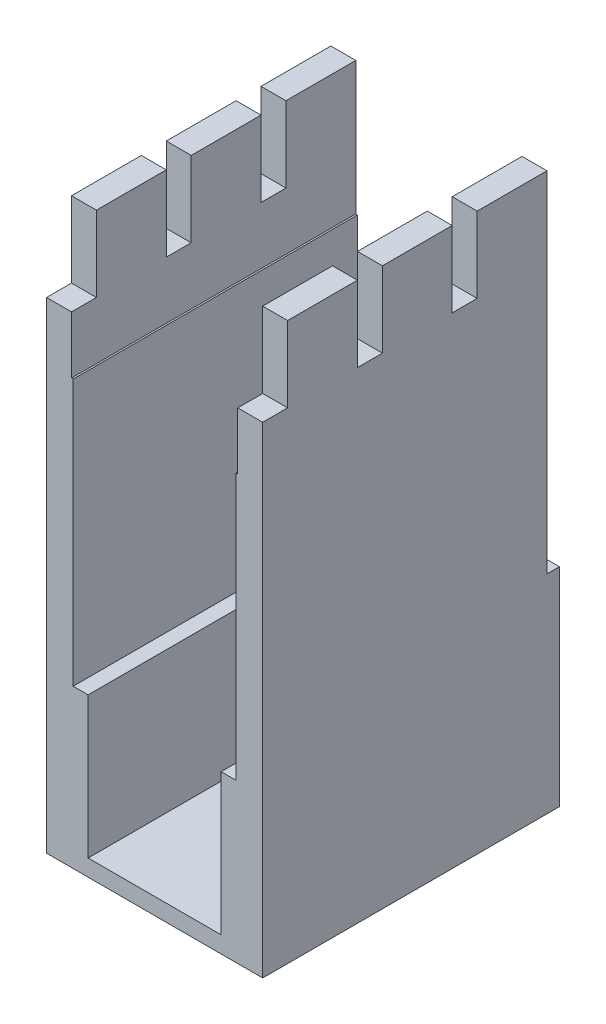
SolidWorks part; units mm, degrees
ref_plane "Front Plane" through (0, 0, 0) normal (0, 0, 1) x (1, 0, 0)
ref_plane "Top Plane" through (0, 0, 0) normal (0, 1, 0) x (1, 0, 0)
ref_plane "Right Plane" through (0, 0, 0) normal (1, 0, 0) x (0, 0, -1)
sketch "Sketch1" plane through (0, 0, 0) normal (0, 0, 1) x (1, 0, 0)
  line L0 (-13, 67) -> (-13, 0)
  line L1 (-13, 0) -> (13, 0)
  line L2 (13, 0) -> (13, 67)
  line L3 (13, 67) -> (10, 67)
  line L4 (10, 67) -> (10, 51)
  line L5 (10, 51) -> (9.8, 51)
  line L9 (-9.8, 51) -> (-10, 51)
  line L10 (-10, 51) -> (-10, 67)
  line L11 (-10, 67) -> (-13, 67)
  line L12 (-9.8, 51) -> (-9.8, 19)
  line L13 (-9.8, 19) -> (-8, 19)
  line L14 (-8, 19) -> (-8, 2)
  line L15 (9.8, 51) -> (9.8, 19)
  line L16 (9.8, 19) -> (8, 19)
  line L17 (8, 19) -> (8, 2)
  line L18 (-8, 2) -> (8, 2)
  point P11 (0, 0)
  point P25 (-11.5, 67)
  dimension "D1" = 2
  dimension "D2" = 3
  dimension "D3" = 20
  dimension "D4" = 19.6
  dimension "D5" = 16
  dimension "D6" = 17
  dimension "D7" = 32
  dimension "D8" = 65
extrude "Boss-Extrude1" add sketch "Sketch1" along normal blind 54
sketch "Sketch2" plane through (13, 0, 0) normal (1, 0, 0) x (0, 0, -1)
  line L0 (-54, 67) -> (0, 67) construction
  line L1 (-45.6, 67) -> (-42.6, 67)
  line L2 (-45.6, 67) -> (-45.6, 57.9)
  line L3 (-45.6, 57.9) -> (-42.6, 57.9)
  line L4 (-42.6, 67) -> (-42.6, 57.9)
  line L5 (-54, 62.45) -> (-45.6, 62.45) construction
  line L6 (-34.2, 67) -> (-31.2, 67)
  line L7 (-34.2, 67) -> (-34.2, 57.9)
  line L8 (-34.2, 57.9) -> (-31.2, 57.9)
  line L9 (-31.2, 67) -> (-31.2, 57.9)
  line L10 (-22.8, 67) -> (-19.8, 67)
  line L11 (-22.8, 67) -> (-22.8, 57.9)
  line L12 (-22.8, 57.9) -> (-19.8, 57.9)
  line L13 (-19.8, 67) -> (-19.8, 57.9)
  line L14 (-11.4, 67) -> (-8.4, 67)
  line L15 (-11.4, 67) -> (-11.4, 57.9)
  line L16 (-11.4, 57.9) -> (-8.4, 57.9)
  line L17 (-8.4, 67) -> (-8.4, 57.9)
  line L18 (-54, 0) -> (-54, 67) construction
  line L19 (-42.6, 62.45) -> (-34.2, 62.45) construction
  line L20 (-31.2, 62.45) -> (-22.8, 62.45) construction
  line L21 (-19.8, 62.45) -> (-11.4, 62.45) construction
  line L22 (-8.4, 62.45) -> (0, 62.45) construction
  line L23 (0, 0) -> (0, 67) construction
  line L24 (-54, 0) -> (0, 0) construction
  line L25 (-54, 67) -> (-34.2, 67)
  line L26 (-54, 67) -> (-54, 0)
  line L27 (-54, 0) -> (-34.2, 0)
  line L28 (-34.2, 67) -> (-34.2, 0)
  line M15 (0, 67) -> (-54, 67)
  line M16 (-54, 67) -> (-54, 0)
  line M17 (-54, 0) -> (0, 0)
  dimension "D1" = 3
  dimension "D2" = 55.9
extrude "Cut-Extrude1" cut sketch "Sketch2" against normal through all contours L28 L7 L4 L3 L2 M15 M16 M17 | L9 L7 L8 M15 | L13 L11 L12 M15 | L17 L15 L16 M15 | L4 L2 L3 M15
sketch "Sketch3" plane through (0, 0, 0) normal (0, 0, -1) x (-1, 0, 0)
  line L0 (13, 67) -> (13, 0) construction
  line L1 (-13, 0) -> (13, 0)
  line L2 (-13, 0) -> (-13, 25)
  line L3 (-13, 25) -> (13, 25)
  line L4 (13, 0) -> (13, 25)
  dimension "D1" = 25
extrude "Boss-Extrude2" add sketch "Sketch3" along normal blind 1.5
